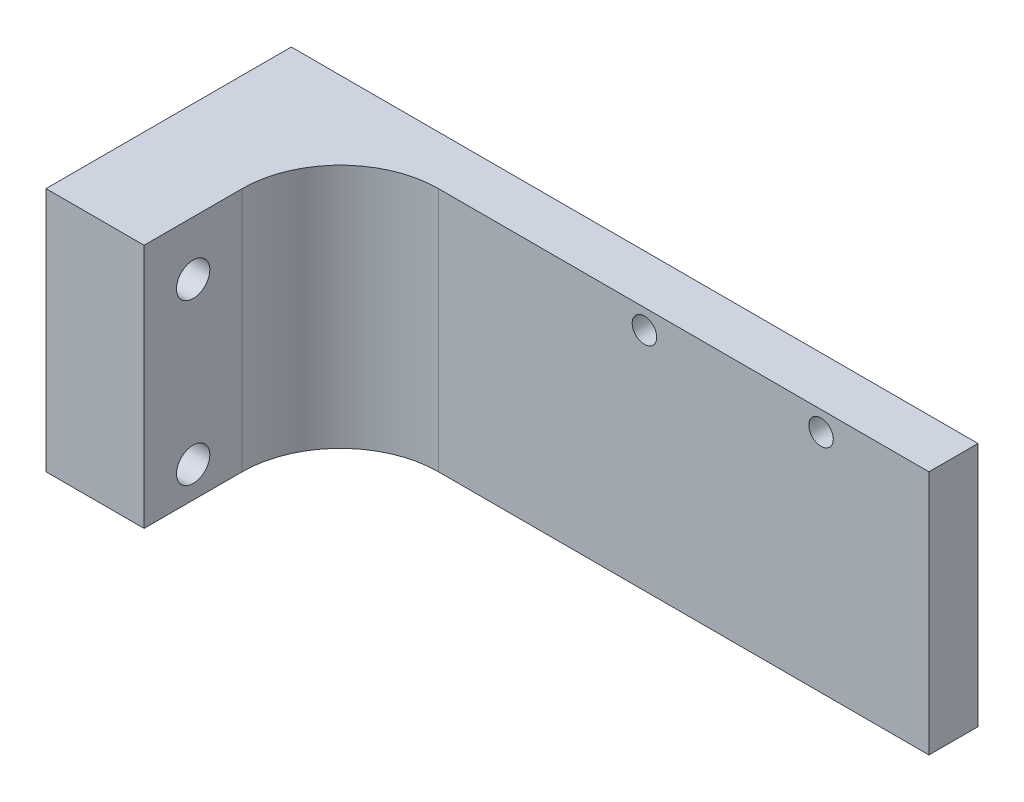
SolidWorks part; units mm, degrees
ref_plane "Front Plane" through (0, 0, 0) normal (0, 0, 1) x (1, 0, 0)
ref_plane "Top Plane" through (0, 0, 0) normal (0, 1, 0) x (1, 0, 0)
ref_plane "Right Plane" through (0, 0, 0) normal (1, 0, 0) x (0, 0, -1)
sketch "Sketch1" plane through (0, 0, 0) normal (0, 0, 1) x (1, 0, 0)
  line L1 (0, 0) -> (70, 0)
  line L2 (0, 0) -> (0, -25)
  line L3 (0, -25) -> (70, -25)
  line L4 (70, 0) -> (70, -25)
  dimension "D1" = 70
  dimension "D2" = 25
extrude "Boss-Extrude1" add sketch "Sketch1" along normal blind 5
sketch "Sketch2" plane through (0, 0, 5) normal (0, 0, 1) x (1, 0, 0)
  line L0 (0, -2) -> (70, -2) construction
  line L1 (0, 0) -> (0, -25) construction
  line L2 (70, -25) -> (70, 0) construction
  line L3 (50, -25) -> (50, 0) construction
  line L6 (30, -25) -> (30, 0) construction
  line L7 (0, -25) -> (70, -25) construction
  line L8 (70, 0) -> (0, 0) construction
  line L9 (70, -25) -> (70, 0) construction
  circle A2 centre (41, -2) radius 1.25
  circle A3 centre (59, -2) radius 1.25
  dimension "D3" = 9
  dimension "D4" = 9
  dimension "D2" = 20
  dimension "D1" = 2
  dimension "D6" = 40
extrude "Cut-Extrude2" cut sketch "Sketch2" against normal through all
sketch "Sketch5" plane through (0, 0, 5) normal (0, 0, 1) x (1, 0, 0)
  line L0 (10, 0) -> (10, -25) construction
  line L1 (70, 0) -> (0, 0) construction
  line L2 (0, -25) -> (70, -25) construction
  line L4 (0, 0) -> (10, 0)
  line L5 (0, 0) -> (0, -25)
  line L6 (0, -25) -> (10, -25)
  line L7 (10, 0) -> (10, -25)
  dimension "D1" = 10
extrude "Boss-Extrude3" add sketch "Sketch5" along normal blind 20
fillet "Fillet1" radius 10 1 edges at (10, -12.5, 5)
sketch "Sketch6" plane through (10, 0, 0) normal (1, 0, 0) x (0, 0, -1)
  line L0 (-20, -25) -> (-20, 0) construction
  line L1 (-25, -25) -> (-15, -25) construction
  line L2 (-25, 0) -> (-15, 0) construction
  circle A0 centre (-20, -21.8349) radius 1.7
  circle A1 centre (-20, -5.5031) radius 1.7
extrude "Cut-Extrude3" cut sketch "Sketch6" against normal through all
